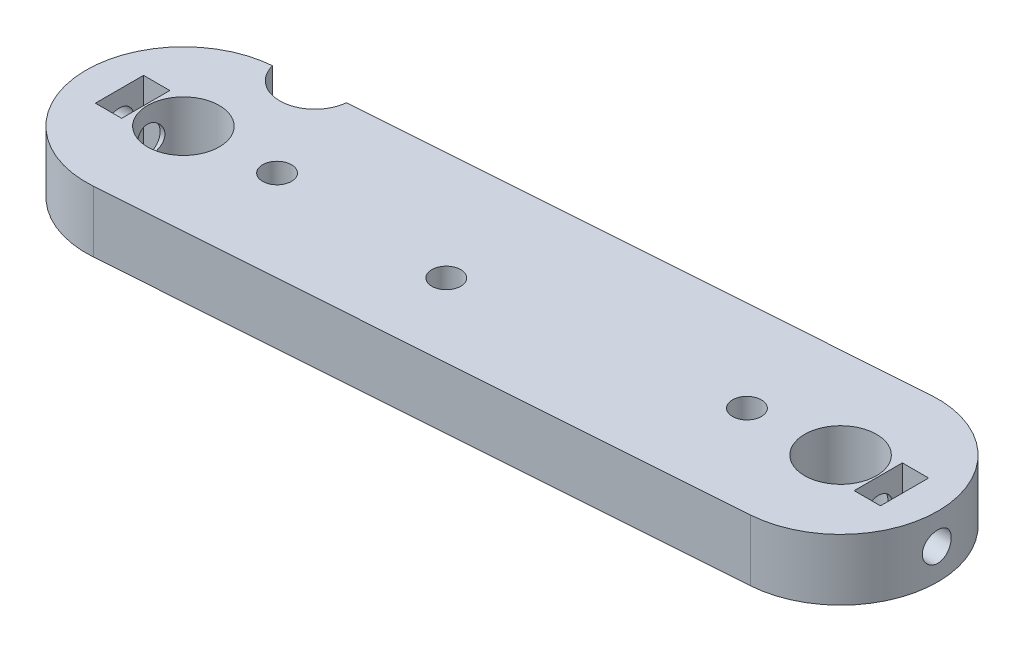
SolidWorks part; units mm, degrees
ref_plane "Plano frontal" through (0, 0, 0) normal (0, 0, 1) x (1, 0, 0)
ref_plane "Plano superior" through (0, 0, 0) normal (0, 1, 0) x (1, 0, 0)
ref_plane "Plano direito" through (0, 0, 0) normal (1, 0, 0) x (0, 0, -1)
sketch "Esboço2" plane through (0, 0, 0) normal (0, 1, 0) x (1, 0, 0)
  line L0 (0, 0) -> (24.9005, 0) construction
  line L1 (-0.7908, 46.0718) -> (69.2092, 51.0718)
  line L2 (-11.1, 35) -> (-11.1, -35)
  line L3 (81.1, 40) -> (81.1, -40)
  line L4 (-0.7908, -46.0718) -> (69.2092, -51.0718)
  line L5 (74.3, -37.25) -> (77.3, -42.75) construction
  line L6 (-4.3, 37.75) -> (-7.3, 37.75)
  line L7 (-4.3, 37.75) -> (-4.3, 32.25)
  line L8 (-4.3, 32.25) -> (-7.3, 32.25)
  line L9 (-7.3, 37.75) -> (-7.3, 32.25)
  line L10 (-4.3, 37.75) -> (-7.3, 32.25) construction
  line L11 (-4.3, 32.25) -> (-7.3, 37.75) construction
  line L12 (74.3, 42.75) -> (77.3, 42.75)
  line L13 (74.3, 42.75) -> (74.3, 37.25)
  line L14 (74.3, 37.25) -> (77.3, 37.25)
  line L15 (77.3, 42.75) -> (77.3, 37.25)
  line L16 (74.3, 42.75) -> (77.3, 37.25) construction
  line L17 (74.3, 37.25) -> (77.3, 42.75) construction
  line L18 (74.3, -42.75) -> (77.3, -37.25) construction
  line L19 (77.3, -42.75) -> (77.3, -37.25)
  line L20 (74.3, -37.25) -> (77.3, -37.25)
  line L21 (74.3, -42.75) -> (74.3, -37.25)
  line L22 (74.3, -42.75) -> (77.3, -42.75)
  line L23 (-4.3, -32.25) -> (-7.3, -37.75) construction
  line L24 (-4.3, -37.75) -> (-7.3, -32.25) construction
  line L25 (-7.3, -37.75) -> (-7.3, -32.25)
  line L26 (-4.3, -32.25) -> (-7.3, -32.25)
  line L27 (-4.3, -37.75) -> (-4.3, -32.25)
  line L28 (-4.3, -37.75) -> (-7.3, -37.75)
  line L29 (0, 35) -> (70, 40) construction
  circle A0 centre (0, 35) radius 4.1
  arc A1 (81.1, -40) -> (69.2092, -51.0718) centre (70, -40) cw
  circle A2 centre (70, 40) radius 4.1
  arc A3 (-0.7908, -46.0718) -> (-11.1, -35) centre (0, -35) cw
  arc A4 (-0.7908, 46.0718) -> (-11.1, 35) centre (0, 35) ccw
  arc A5 (81.1, 40) -> (69.2092, 51.0718) centre (70, 40) ccw
  circle A6 centre (70, -40) radius 4.1
  circle A7 centre (0, -35) radius 4.1
  circle A8 centre (9.9746, 35.7125) radius 1.65
  circle A9 centre (60.0254, 39.2875) radius 1.65
  circle A10 centre (9.9746, -35.7125) radius 1.65
  circle A11 centre (60.0254, -39.2875) radius 1.65
  circle A12 centre (30, 35) radius 1.65
  circle A13 centre (30, -35) radius 1.65
  point P5 (75.8, 40)
  point P16 (-5.8, 35)
  point P18 (-11.1, 0)
  point P25 (81.1, 0)
  point P35 (75.8, -40)
  point P40 (-5.8, -35)
  dimension "D1" = 8.2
  dimension "D2" = 8.2
  dimension "D12" = 3.3
  dimension "D5" = 70
  dimension "D6" = 7
  dimension "D7" = 7
  dimension "D4" = 70
  dimension "D8" = 5.5
  dimension "D9" = 3
  dimension "D10" = 0.2
  dimension "D11" = 0.2
  dimension "D3" = 80
  dimension "D13" = 10
  dimension "D14" = 10
  dimension "D15" = 30
extrude "Ressalto-extrusão1" add sketch "Esboço2" along normal blind 7
sketch "Esboço3" plane through (0, 7, 0) normal (0, 1, 0) x (1, 0, 0)
  line L0 (0.7908, 23.9282) -> (70.7908, 28.9282)
  line L1 (-0.7908, 46.0718) -> (69.2092, 51.0718)
  line L3 (-18.4816, -52.8475) -> (99.2851, -52.8475)
  line L4 (-18.4816, -52.8475) -> (-18.4816, 52.8475)
  line L5 (-18.4816, 52.8475) -> (99.2851, 52.8475)
  line L6 (99.2851, -52.8475) -> (99.2851, 52.8475)
  line L7 (-18.4816, -52.8475) -> (99.2851, 52.8475) construction
  line L8 (-18.4816, 52.8475) -> (99.2851, -52.8475) construction
  arc A0 (-0.7908, 46.0718) -> (0.7908, 23.9282) centre (0, 35) ccw
  arc A1 (70.7908, 28.9282) -> (69.2092, 51.0718) centre (70, 40) ccw
  point P1 (40.4017, 0)
extrude "Corte-extrusão1" cut sketch "Esboço3" against normal through all both and the other way through all
sketch "Esboço4" plane through (-4.3, 0, 0) normal (-1, 0, 0) x (0, 0, 1)
  line L0 (-35, 7) -> (-35, 0) construction
  line L1 (-32.25, 7) -> (-37.75, 7) construction
  line L2 (-32.25, 0) -> (-37.75, 0) construction
  circle A0 centre (-35, 3.5) radius 1.65
  dimension "D1" = 3.3
extrude "Corte-extrusão2" cut sketch "Esboço4" along normal through all and the other way blind 2
sketch "Esboço5" plane through (74.3, 0, 0) normal (1, 0, 0) x (0, 0, -1)
  line L0 (40, 0) -> (40, 7) construction
  line L1 (42.75, 0) -> (37.25, 0) construction
  line L2 (42.75, 7) -> (37.25, 7) construction
  circle A0 centre (40, 3.5) radius 1.65
  dimension "D1" = 3.3
extrude "Corte-extrusão3" cut sketch "Esboço5" along normal blind 10 and the other way blind 2
sketch "Esboço6" plane through (0, 7, 0) normal (0, 1, 0) x (1, 0, 0)
  circle A0 centre (3, 47) radius 4
  circle A1 centre (0, 35) radius 4.1 construction
  dimension "D3" = 8
  dimension "D1" = 12
  dimension "D2" = 3
extrude "Corte-extrusão4" cut sketch "Esboço6" against normal through all both and the other way through all
equation "\"D7@Esboço2\"=\"D6@Esboço2\""
equation "\"D14@Esboço2\"=\"D13@Esboço2\""
equation "\"D2@Esboço2\"=\"D1@Esboço2\""
